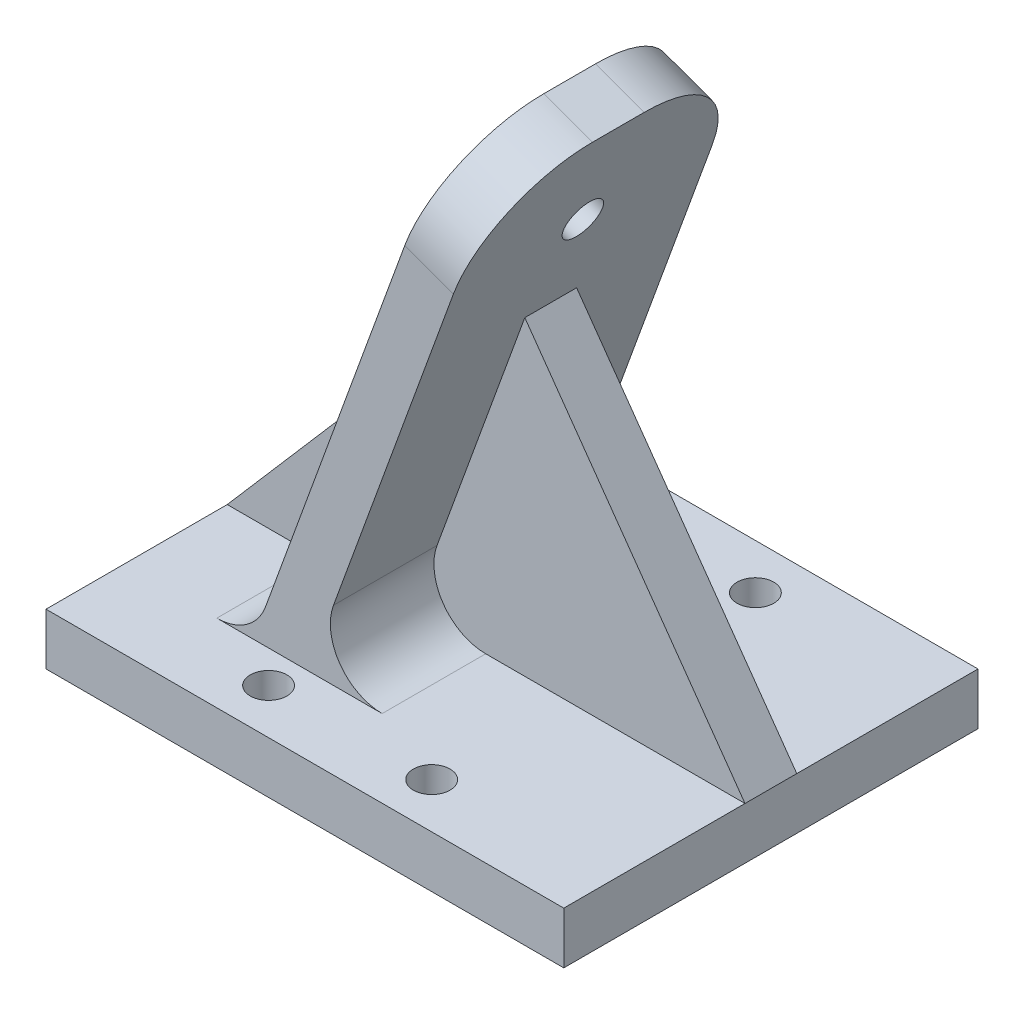
SolidWorks part; units mm, degrees
material "PLA Black"
ref_plane "Front Plane" through (0, 0, 0) normal (0, 0, 1) x (1, 0, 0)
ref_plane "Top Plane" through (0, 0, 0) normal (0, 1, 0) x (1, 0, 0)
ref_plane "Right Plane" through (0, 0, 0) normal (1, 0, 0) x (0, 0, -1)
sketch "Sketch1" plane through (0, 0, 0) normal (0, 1, 0) x (1, 0, 0)
  line L1 (-31.75, -25.4) -> (31.75, -25.4)
  line L2 (-31.75, -25.4) -> (-31.75, 25.4)
  line L3 (-31.75, 25.4) -> (31.75, 25.4)
  line L4 (31.75, -25.4) -> (31.75, 25.4)
  line L5 (-31.75, -25.4) -> (31.75, 25.4) construction
  line L6 (-31.75, 25.4) -> (31.75, -25.4) construction
  point P0 (0, 0)
  dimension "D1" = 63.5
  dimension "D2" = 50.8
extrude "Boss-Extrude1" add sketch "Sketch1" along normal blind 6.35
sketch "Sketch2" plane through (0, 0, 0) normal (0, 0, 1) x (1, 0, 0)
  line L0 (-11.43, 0) -> (13.0366, 67.2214)
  line L1 (-11.43, 0) -> (-17.397, 2.1718)
  line L2 (13.0366, 67.2214) -> (7.0695, 69.3932)
  line L3 (-17.397, 2.1718) -> (7.0695, 69.3932)
  line L4 (-11.43, 0) -> (7.0695, 69.3932) construction
  line L5 (13.0366, 67.2214) -> (-17.397, 2.1718) construction
  line L6 (31.75, 6.35) -> (31.75, 0) construction
  line L7 (-31.75, 0) -> (31.75, 0) construction
  point P1 (-2.1802, 34.6966)
  dimension "D1" = 20
  dimension "D2" = 50.8
  dimension "D3" = 11.43
extrude "Boss-Extrude2" add sketch "Sketch2" against normal mid plane 31.75
fillet "Fillet1" radius 12.7 2 edges at (10.0531, 68.3073, 15.875) (10.0531, 68.3073, -15.875)
sketch "Sketch5" plane through (-16.06, 5.8454, 0) normal (-0.9397, 0.342, 0) x (0, 0, 1)
  line L0 (-3.175, 67.6262) -> (3.175, 67.6262) construction
  circle A0 centre (0, 54.9262) radius 2.413
  point P6 (0, 67.6262)
  dimension "D1" = 4.826
  dimension "D2" = 12.7
fillet "Fillet2" radius 6.35 2 edges at (-15.8763, 6.35, 0) (-9.1188, 6.35, 0)
sketch "Sketch7" plane through (0, 0, 0) normal (0, 0, 1) x (1, 0, 0)
  line L0 (4.7485, 44.45) -> (31.75, 6.35)
  line L2 (-31.75, 6.35) -> (31.75, 6.35) construction
  line L3 (-31.75, 6.35) -> (-20.3226, 6.35)
  line L7 (-31.75, 6.35) -> (-4.3203, 38.1)
  line L8 (2.7259, 57.4591) -> (-14.3556, 10.5282) construction
  line L10 (-4.3203, 38.1) -> (-14.3556, 10.5282)
  line L12 (-0.05, 6.35) -> (31.75, 6.35)
  line L13 (-6.0171, 14.8718) -> (4.7485, 44.45)
  line L14 (-6.0171, 14.8718) -> (8.6929, 55.2873) construction
  arc A0 (-6.0171, 14.8718) -> (-0.05, 6.35) centre (-0.05, 12.7) ccw construction
  arc A4 (-20.3226, 6.35) -> (-14.3556, 10.5282) centre (-20.3226, 12.7) ccw construction
  arc A5 (-6.0171, 14.8718) -> (-0.05, 6.35) centre (-0.05, 12.7) ccw
  arc A6 (-20.3226, 6.35) -> (-14.3556, 10.5282) centre (-20.3226, 12.7) ccw
  dimension "D1" = 31.75
  dimension "D2" = 38.1
extrude "Boss-Extrude5" add sketch "Sketch7" along normal mid plane 6.35
extrude "Cut-Extrude3" cut sketch "Sketch5" against normal through all
sketch "Sketch8" plane through (0, 6.35, 0) normal (0, 1, 0) x (1, 0, 0)
  line L4 (-10, -19.85) -> (10, 19.85) construction
  circle A0 centre (10, -19.85) radius 2.25
  circle A1 centre (10, 19.85) radius 2.25
  circle A2 centre (-10, 19.85) radius 2.25
  circle A3 centre (-10, -19.85) radius 2.25
  point P8 (0, 0)
  dimension "D2" = 4.5
  dimension "D1" = 39.7
  dimension "D5" = 20
extrude "Cut-Extrude4" cut sketch "Sketch8" against normal through all
